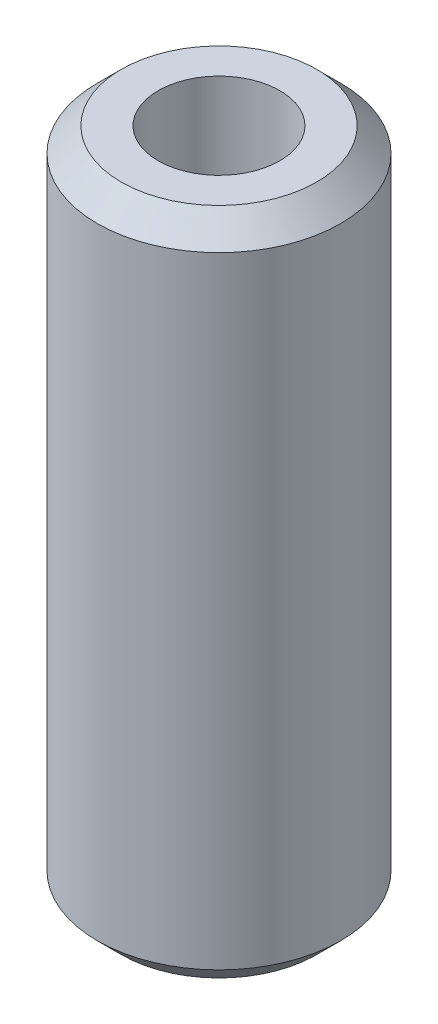
SolidWorks part; units mm, degrees
ref_plane "Front Plane" through (0, 0, 0) normal (0, 0, 1) x (1, 0, 0)
ref_plane "Top Plane" through (0, 0, 0) normal (0, 1, 0) x (1, 0, 0)
ref_plane "Right Plane" through (0, 0, 0) normal (1, 0, 0) x (0, 0, -1)
sketch "Sketch1" plane through (0, 0, 0) normal (0, 1, 0) x (1, 0, 0)
  circle A0 centre (0, 0) radius 6.35
  circle A1 centre (0, 0) radius 12.7
  dimension "D1" = 12.7
  dimension "D2" = 25.4
extrude "Boss-Extrude1" add sketch "Sketch1" along normal mid plane 69.85
chamfer "Chamfer1" distance 2.5 angle 45 2 edges at (0, -34.925, 12.7) (0, 34.925, 12.7)
